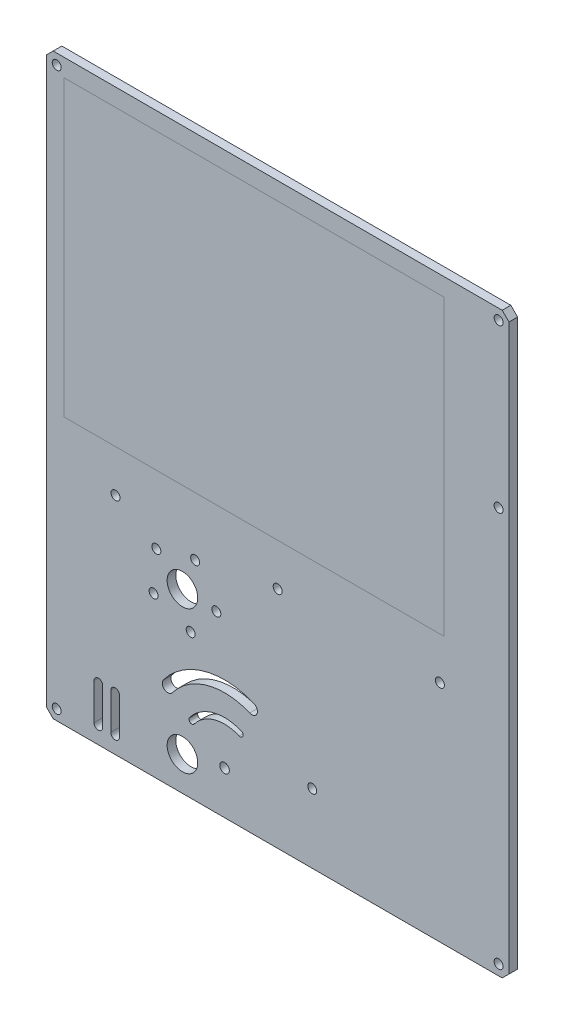
SolidWorks part; units mm, degrees
ref_plane "Front Plane" through (0, 0, 0) normal (0, 0, 1) x (1, 0, 0)
ref_plane "Top Plane" through (0, 0, 0) normal (0, 1, 0) x (1, 0, 0)
ref_plane "Right Plane" through (0, 0, 0) normal (1, 0, 0) x (0, 0, -1)
sketch "Sketch1" plane through (0, 0, 0) normal (0, 0, 1) x (1, 0, 0)
  line L1 (0, 0) -> (340, 0)
  line L2 (0, 0) -> (0, 425)
  line L3 (0, 425) -> (340, 425)
  line L4 (340, 0) -> (340, 425)
  dimension "D1" = 340
  dimension "D2" = 425
extrude "Boss-Extrude1" add sketch "Sketch1" along normal blind 6.35
sketch "Sketch2" plane through (0, 0, 6.35) normal (0, 0, 1) x (1, 0, 0)
  line L0 (340, 425) -> (0, 425) construction
  line L1 (292.4, 412) -> (13, 412) construction
  line L2 (292.4, 412) -> (292.4, 196.1)
  line L3 (292.4, 196.1) -> (13, 196.1)
  line L4 (13, 412) -> (13, 196.1)
  line L6 (0, 425) -> (0, 0) construction
  line L8 (13, 412) -> (292.4, 412)
  line L9 (13, 412) -> (13, 259.6) construction
  line L10 (13, 259.6) -> (292.4, 259.6) construction
  line L11 (292.4, 412) -> (292.4, 259.6) construction
  dimension "D1" = 215.9
  dimension "D2" = 279.4
  dimension "D3" = 13
  dimension "D4" = 13
  dimension "D5" = 152.4
sketch "Sketch3" plane through (0, 0, 6.35) normal (0, 0, 1) x (1, 0, 0)
  line L0 (0, 425) -> (0, 0) construction
  line L3 (0, 0) -> (340, 0) construction
  circle A0 centre (100, 130) radius 11.25
  circle A1 centre (100, 25) radius 11.25
  dimension "D1" = 22.5
  dimension "D2" = 22.5
  dimension "D4" = 100
  dimension "D3" = 105
  dimension "D5" = 25
extrude "Cut-Extrude1" cut sketch "Sketch3" against normal through all
sketch "Sketch5" plane through (0, 0, 6.35) normal (0, 0, 1) x (1, 0, 0)
  line L0 (89.2796, 62.7765) -> (130.9639, 31.6892) construction
  line L1 (151.014, 79.6683) -> (130.9639, 31.6892) construction
  circle A2 centre (130.9639, 31.6892) radius 3.5223
  arc A3 (106.9153, 49.6242) -> (142.5313, 59.3694) centre (130.9639, 31.6892) cw construction
  arc A4 (89.2796, 62.7765) -> (151.014, 79.6683) centre (130.9639, 31.6892) cw construction
  arc A5 (108.5987, 48.3687) -> (141.7216, 57.4318) centre (130.9639, 31.6892) cw
  arc A6 (105.2319, 50.8796) -> (143.341, 61.307) centre (130.9639, 31.6892) cw
  arc A7 (108.5987, 48.3687) -> (105.2319, 50.8796) centre (106.9153, 49.6242) cw
  arc A8 (141.7216, 57.4318) -> (143.341, 61.307) centre (142.5313, 59.3694) ccw
  arc A9 (92.5663, 60.3254) -> (149.4332, 75.8853) centre (130.9639, 31.6892) cw
  arc A10 (85.993, 65.2276) -> (152.5949, 83.4512) centre (130.9639, 31.6892) cw
  arc A11 (92.5663, 60.3254) -> (85.993, 65.2276) centre (89.2796, 62.7765) cw
  arc A12 (149.4332, 75.8853) -> (152.5949, 83.4512) centre (151.014, 79.6683) ccw
  point P0 (89.2796, 61.307)
  point P8 (123.0463, 60.6255)
  point P20 (117.2401, 81.8455)
  dimension "D1" = 30
  dimension "D2" = 22
  dimension "D3" = 2.1
  dimension "D4" = 2.1
  dimension "D5" = 4.1
  dimension "D6" = 4.1
extrude "Cut-Extrude2" cut sketch "Sketch5" against normal blind 10
sketch "Sketch6" plane through (0, 0, 6.35) normal (0, 0, 1) x (1, 0, 0)
  line L0 (38.2141, 39.2968) -> (38.2141, 12.5) construction
  line L1 (41.3891, 39.2968) -> (41.3891, 12.5)
  line L2 (35.0391, 39.2968) -> (35.0391, 12.5)
  line L3 (44.372, 39.8963) -> (44.372, 10.1037) construction
  line L8 (33.1916, 10.1037) -> (55.5524, 10.1037) construction
  line L9 (55.5524, 18.1037) -> (33.1916, 18.1037) construction
  line L10 (55.5524, 39.8963) -> (33.1916, 39.8963) construction
  line L11 (33.1916, 31.8963) -> (55.5524, 31.8963) construction
  line L12 (33.1916, 10.1037) -> (55.5524, 10.1037) construction
  line L13 (55.5524, 18.1037) -> (33.1916, 18.1037) construction
  line L14 (55.5524, 39.8963) -> (33.1916, 39.8963) construction
  line L15 (33.1916, 31.8963) -> (55.5524, 31.8963) construction
  line L18 (50.5299, 39.2968) -> (50.5299, 12.5) construction
  line L19 (47.3549, 39.2968) -> (47.3549, 12.5)
  line L20 (53.7049, 39.2968) -> (53.7049, 12.5)
  arc A0 (41.3891, 39.2968) -> (35.0391, 39.2968) centre (38.2141, 39.2968) ccw
  arc A1 (35.0391, 12.5) -> (41.3891, 12.5) centre (38.2141, 12.5) ccw
  arc A8 (33.1916, 39.8963) -> (33.1916, 31.8963) centre (33.1916, 35.8963) ccw construction
  arc A9 (33.1916, 39.8963) -> (33.1916, 31.8963) centre (33.1916, 35.8963) ccw construction
  arc A10 (33.1916, 18.1037) -> (33.1916, 10.1037) centre (33.1916, 14.1037) ccw construction
  arc A11 (33.1916, 18.1037) -> (33.1916, 10.1037) centre (33.1916, 14.1037) ccw construction
  arc A24 (47.3549, 39.2968) -> (53.7049, 39.2968) centre (50.5299, 39.2968) cw
  arc A25 (53.7049, 12.5) -> (47.3549, 12.5) centre (50.5299, 12.5) cw
  arc A26 (55.5524, 18.1037) -> (55.5524, 10.1037) centre (55.5524, 14.1037) cw construction
  arc A27 (55.5524, 39.8963) -> (55.5524, 31.8963) centre (55.5524, 35.8963) cw construction
  point P14 (50.5299, 25.8984)
  point P17 (38.2141, 25.8984)
  point P27 (18.1916, 25.2362)
  point P29 (21.0985, 25.7907)
  point P30 (39.4258, 26.1938)
  point P31 (38.2141, 25.8984)
  dimension "D1" = 6.35
extrude "Cut-Extrude3" cut sketch "Sketch6" against normal blind 17
split line "Split Line1"
sketch "Sketch7" plane through (0, 0, 6.35) normal (0, 0, 1) x (1, 0, 0)
  circle A0 centre (100, 130) radius 11.25 construction
  circle A1 centre (100, 130) radius 11.25 construction
  dimension "D1" = 66.1
  dimension "D2" = 87
sketch "Sketch8" plane through (0, 0, 6.35) normal (0, 0, 1) x (1, 0, 0)
  line L0 (0, 425) -> (0, 0) construction
  line L1 (340, 425) -> (0, 425) construction
  line L2 (340, 0) -> (340, 425) construction
  line L3 (0, 0) -> (340, 0) construction
  circle A0 centre (332.38, 417.38) radius 3.302
  circle A1 centre (7.62, 417.38) radius 3.302
  circle A2 centre (50.8, 165.1) radius 3.302
  circle A3 centre (332.38, 7.62) radius 3.302
  circle A4 centre (195.4, 50.8) radius 3.302
  circle A5 centre (289.2, 165.1) radius 3.302
  circle A6 centre (170, 165.1) radius 3.302
  circle A7 centre (332.38, 298) radius 3.302
  circle A8 centre (7.62, 7.62) radius 3.302
  point P19 (170, 0)
  dimension "D1" = 6.604
  dimension "D12" = 7.62
  dimension "D15" = 6.604
  dimension "D2" = 7.62
  dimension "D3" = 7.62
  dimension "D4" = 7.62
  dimension "D5" = 7.62
  dimension "D6" = 7.62
  dimension "D7" = 50.8
  dimension "D8" = 165.1
  dimension "D9" = 50.8
  dimension "D10" = 25.4
  dimension "D11" = 50.8
  dimension "D13" = 127
  dimension "D14" = 7.62
extrude "Cut-Extrude4" cut sketch "Sketch8" against normal through all
sketch "Sketch9" plane through (0, 0, 6.35) normal (0, 0, 1) x (1, 0, 0)
  circle A0 centre (78.8123, 116.7305) radius 3.302 construction
  circle A1 centre (80.8326, 146.0502) radius 3.302 construction
  circle A2 centre (109.3416, 153.1891) radius 3.302 construction
  circle A3 centre (124.9409, 128.2815) radius 3.302 construction
  circle A4 centre (106.0727, 105.7488) radius 3.302 construction
  circle A5 centre (78.8123, 116.7305) radius 3.302
  circle A6 centre (80.8326, 146.0502) radius 3.302
  circle A7 centre (109.3416, 153.1891) radius 3.302
  circle A8 centre (124.9409, 128.2815) radius 3.302
  circle A9 centre (106.0727, 105.7488) radius 3.302
extrude "Cut-Extrude5" cut sketch "Sketch9" against normal through all
chamfer "Chamfer1" distance 5 angle 45 4 edges at (0, 0, 3.175) (340, 0, 3.175) (0, 425, 3.175) (340, 425, 3.175)
